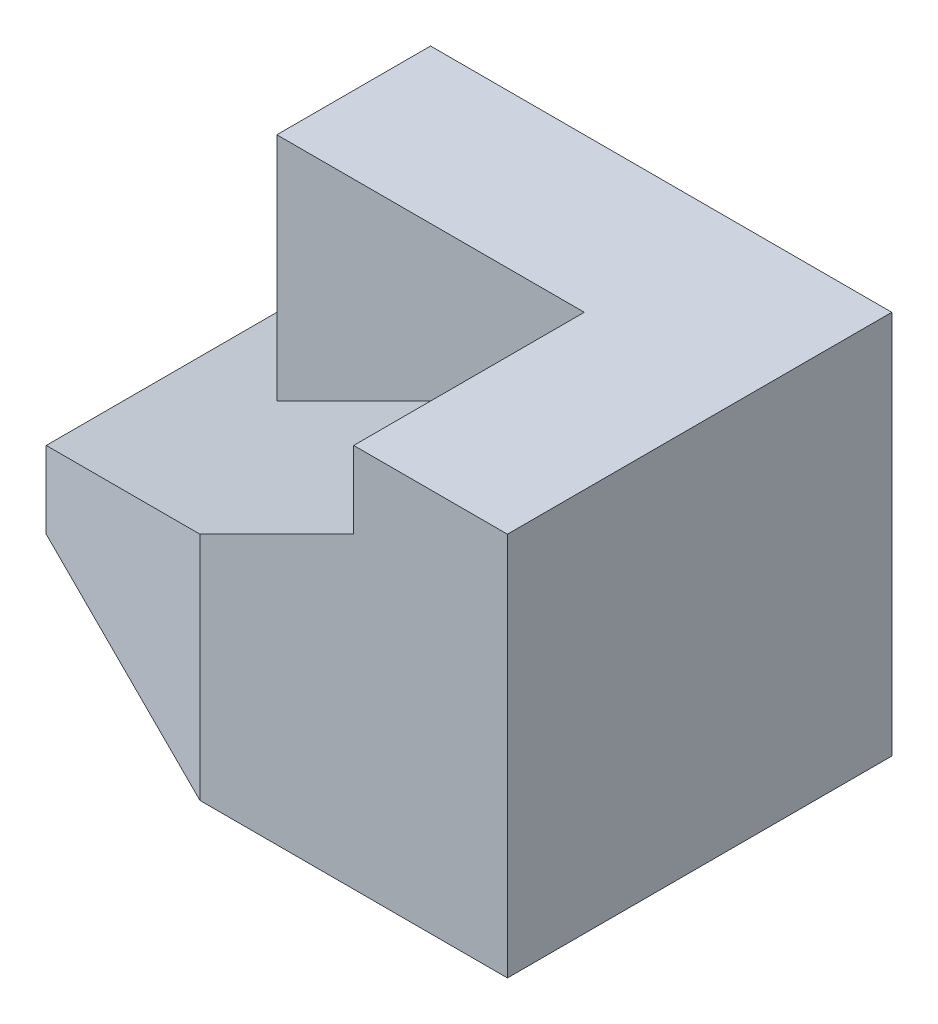
SolidWorks part; units mm, degrees
ref_plane "Front Plane" through (0, 0, 0) normal (0, 0, 1) x (1, 0, 0)
ref_plane "Top Plane" through (0, 0, 0) normal (0, 1, 0) x (1, 0, 0)
ref_plane "Right Plane" through (0, 0, 0) normal (1, 0, 0) x (0, 0, -1)
sketch "Sketch1" plane through (0, 0, 0) normal (0, 0, 1) x (1, 0, 0)
  line L1 (0, 0) -> (80, 0)
  line L2 (0, 0) -> (0, 50)
  line L3 (0, 50) -> (80, 50)
  line L4 (80, 0) -> (80, 50)
  dimension "D1" = 80
  dimension "D2" = 50
extrude "Boss-Extrude1" add sketch "Sketch1" against normal blind 50
sketch "Sketch2" plane through (0, 0, 0) normal (0, 0, 1) x (1, 0, 0)
  line L0 (80, 50) -> (60, 50)
  line L1 (80, 50) -> (0, 50) construction
  line L2 (60, 50) -> (60, 40)
  line L3 (60, 40) -> (40, 30)
  line L4 (40, 30) -> (40, 50)
  line L5 (40, 50) -> (60, 50)
  line M4 (80, 50) -> (0, 50)
  dimension "D1" = 20
  dimension "D2" = 10
  dimension "D3" = 20
  dimension "D4" = 10
extrude "Cut-Extrude1" cut sketch "Sketch2" against normal blind 30 contours L4 L3 L2 M4
sketch "Sketch3" plane through (0, 0, -50) normal (0, 0, -1) x (-1, 0, 0)
  line L1 (0, 50) -> (-20, 50)
  line L2 (0, 50) -> (0, 10)
  line L3 (0, 10) -> (-20, 10)
  line L4 (-20, 50) -> (-20, 10)
  dimension "D1" = 10
  dimension "D2" = 20
extrude "Cut-Extrude2" cut sketch "Sketch3" against normal blind 103
sketch "Sketch4" plane through (0, 0, 0) normal (0, -1, 0) x (-1, 0, 0)
  line L0 (0, 0) -> (0, 20)
  line L1 (0, 50) -> (0, 0) construction
  line L2 (0, 20) -> (-40, 0)
  line L3 (0, 0) -> (-80, 0) construction
  line L4 (-40, 0) -> (0, 0)
  dimension "D1" = 20
  dimension "D2" = 40
extrude "Cut-Extrude3" cut sketch "Sketch4" against normal blind 103
sketch "Sketch5" plane through (40, 0, 0) normal (1, 0, 0) x (0, 0, -1)
  line L1 (30, 50) -> (0, 50)
  line L2 (30, 50) -> (30, 30)
  line L3 (30, 30) -> (0, 30)
  line L4 (0, 50) -> (0, 30)
extrude "Cut-Extrude4" cut sketch "Sketch5" against normal blind 103
ref_plane "Plane1" through (-4, 8, 0) normal (0.4472, -0.8944, 0) x (-0.8944, -0.4472, 0)
sketch "Sketch6" plane through (-4, 8, 0) normal (0.4472, -0.8944, 0) x (-0.8944, -0.4472, 0)
  line L0 (-71.5542, 30) -> (-4.4721, 35)
  line L1 (-4.4721, 20) -> (-4.4721, 50) construction
  line L2 (-71.5542, 30) -> (-71.5542, 0)
  line L3 (-71.5542, 0) -> (0, 0)
  line L4 (0, 0) -> (-4.4721, 35)
extrude "Cut-Extrude6" cut sketch "Sketch6" against normal blind 103
sketch "Sketch7" plane through (-4, 8, 0) normal (0.4472, -0.8944, 0) x (-0.8944, -0.4472, 0)
  line L0 (-26.8328, 33.3333) -> (-4.4721, 50)
  line L1 (-4.4721, 50) -> (-4.4721, 20)
  line L2 (-4.4721, 20) -> (-26.8328, 10)
  line L3 (-26.8328, 33.3333) -> (-26.8328, 50)
  line L4 (-26.8328, 50) -> (-4.4721, 50)
  line L5 (-26.8328, 33.3333) -> (-26.8328, 10)
extrude "Boss-Extrude2" add sketch "Sketch7" along normal blind 15 contours L0 L5 L2 L1 | L4 L3 L0
sketch "Sketch8" plane through (8, 0, -16) normal (-0.4472, 0, 0.8944) x (0.8944, 0, 0.4472)
  line L0 (13.4164, 10) -> (-8.9443, 10)
  line L1 (-8.9443, 10) -> (13.4164, 20)
  line L2 (13.4164, 20) -> (13.4164, 10)
extrude "Boss-Extrude3" add sketch "Sketch8" against normal blind 15
sketch "Sketch10" plane through (0, 0, 0) normal (0, -1, 0) x (-1, 0, 0)
  line L1 (-80, 50) -> (3.8488, 50)
  line L2 (-80, 50) -> (-80, 0)
  line L3 (-80, 0) -> (3.8488, 0)
  line L4 (3.8488, 50) -> (3.8488, 0)
  dimension "D1" = 50
  dimension "D2" = 83.8488
extrude "Cut-Extrude7" cut sketch "Sketch10" along normal blind 15
sketch "Sketch15" plane through (0, 50, 0) normal (0, 1, 0) x (1, 0, 0)
  line L0 (60, 30) -> (20, 30)
  line L1 (20, 32.3333) -> (20, 30)
  line L3 (20, 30) -> (62.9075, 30)
  line L4 (20, 30) -> (20, 35.5671)
  line L5 (20, 35.5671) -> (62.9075, 35.5671)
  line L6 (62.9075, 30) -> (62.9075, 35.5671)
  line M8 (20, 32.3333) -> (55, 30)
  line M9 (55, 30) -> (60, 30)
  line M14 (20, 50) -> (20, 32.3333)
  dimension "D1" = 2.3333
  dimension "D2" = 5.5671
  dimension "D3" = 42.9075
extrude "Boss-Extrude6" add sketch "Sketch15" against normal blind 37 contours L3 L6 L5 M14 M8 M9 | L1 L0 M8
